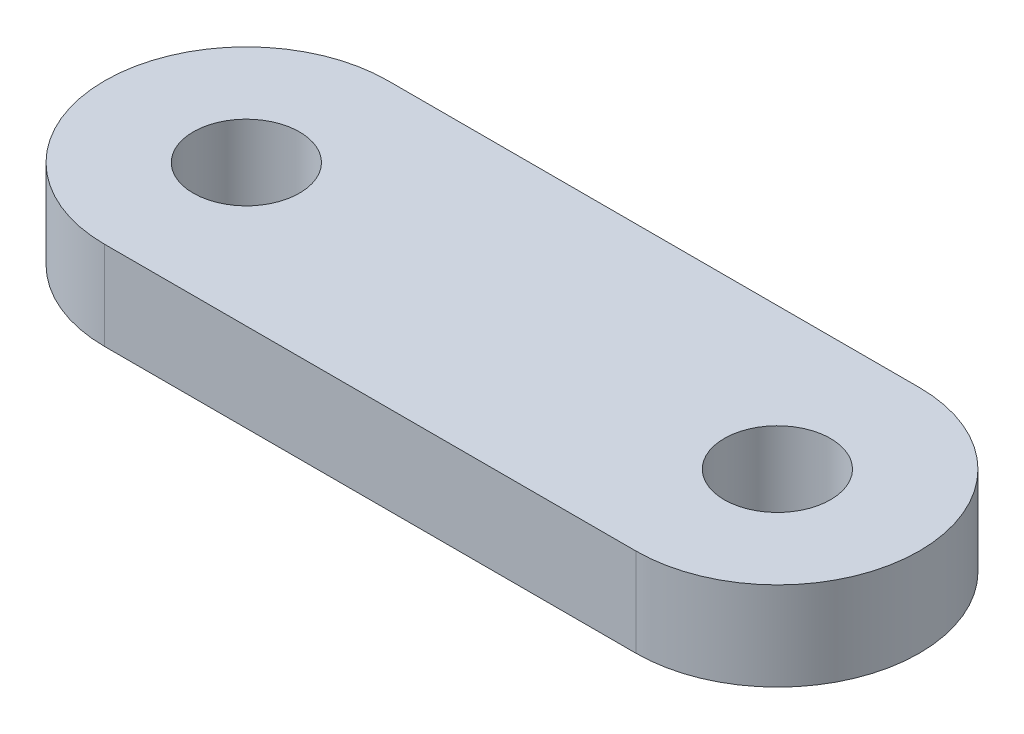
SolidWorks part; units mm, degrees
ref_plane "Front Plane" through (0, 0, 0) normal (0, 0, 1) x (1, 0, 0)
ref_plane "Top Plane" through (0, 0, 0) normal (0, 1, 0) x (1, 0, 0)
ref_plane "Right Plane" through (0, 0, 0) normal (1, 0, 0) x (0, 0, -1)
sketch "Sketch1" plane through (0, 0, 0) normal (0, 1, 0) x (1, 0, 0)
  line L0 (0, 0) -> (15, 0) construction
  line L1 (0, 4) -> (15, 4)
  line L2 (0, -4) -> (15, -4)
  arc A0 (0, 4) -> (0, -4) centre (0, 0) ccw
  arc A1 (15, -4) -> (15, 4) centre (15, 0) ccw
  point P3 (7.5, 0)
  dimension "D2" = 4
  dimension "D1" = 15
extrude "Boss-Extrude1" add sketch "Sketch1" along normal blind 2.5
sketch "Sketch2" plane through (0, 2.5, 0) normal (0, 1, 0) x (1, 0, 0)
  circle A0 centre (0, 0) radius 1.5
  circle A1 centre (14.9931, 0) radius 1.5
  dimension "D1" = 3
  dimension "D2" = 3
extrude "Cut-Extrude1" cut sketch "Sketch2" against normal up to surface (2.5 mm away) up to face at (7.5, 0, 0)
